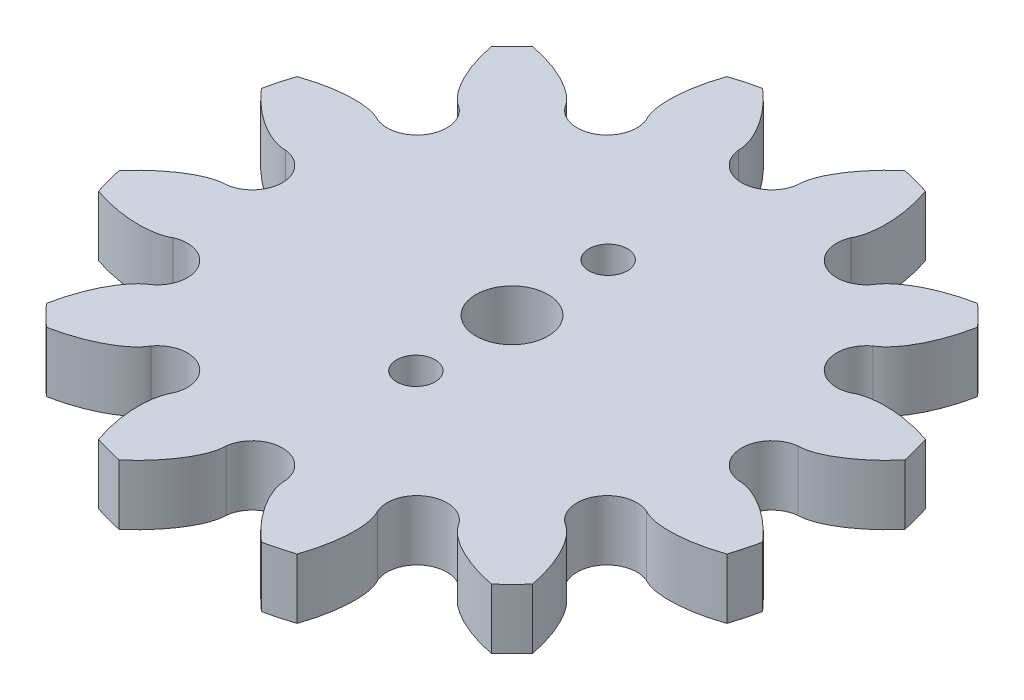
SolidWorks part; units mm, degrees
material "Gerais  - 6061-T6"
ref_plane "Plano frontal" through (0, 0, 0) normal (0, 0, 1) x (1, 0, 0)
ref_plane "Plano superior" through (0, 0, 0) normal (0, 1, 0) x (1, 0, 0)
ref_plane "Plano direito" through (0, 0, 0) normal (1, 0, 0) x (0, 0, -1)
ref_plane "Plano1" through (0, -5, 0) normal (0, -1, 0) x (1, 0, 0)
sketch "Esboço1" plane through (0, -5, 0) normal (0, -1, 0) x (1, 0, 0)
  arc A0 (-19.6917, 75.4926) -> (-17.2134, 71.2002) centre (-18.7058, 73.2002) cw
  arc A1 (-20.2254, 65.4903) -> (-18.5097, 63.7746) centre (0, 84) ccw
  arc A2 (-12.7998, 66.7866) -> (-8.5074, 64.3083) centre (-10.7998, 65.2942) cw
  arc A3 (-8.2609, 57.8575) -> (-5.9171, 57.2295) centre (0, 84) ccw
  arc A4 (-2.4783, 62.6928) -> (2.4783, 62.6928) centre (0, 62.4004) cw
  arc A5 (5.9171, 57.2295) -> (8.2609, 57.8575) centre (0, 84) ccw
  arc A6 (8.5074, 64.3083) -> (12.7998, 66.7866) centre (10.7998, 65.2942) cw
  arc A7 (18.5097, 63.7746) -> (20.2254, 65.4903) centre (0, 84) ccw
  arc A8 (17.2134, 71.2002) -> (19.6917, 75.4926) centre (18.7058, 73.2002) cw
  arc A9 (26.1425, 75.7391) -> (26.7705, 78.0829) centre (0, 84) ccw
  arc A10 (21.3072, 81.5217) -> (21.3072, 86.4783) centre (21.5996, 84) cw
  arc A11 (26.7705, 89.9171) -> (26.1425, 92.2609) centre (0, 84) ccw
  arc A12 (19.6917, 92.5074) -> (17.2134, 96.7998) centre (18.7058, 94.7998) cw
  arc A13 (20.2254, 102.5097) -> (18.5097, 104.2254) centre (0, 84) ccw
  arc A14 (12.7998, 101.2134) -> (8.5074, 103.6917) centre (10.7998, 102.7058) cw
  arc A15 (8.2609, 110.1425) -> (5.9171, 110.7705) centre (0, 84) ccw
  arc A16 (2.4783, 105.3072) -> (-2.4783, 105.3072) centre (0, 105.5996) cw
  arc A17 (-5.9171, 110.7705) -> (-8.2609, 110.1425) centre (0, 84) ccw
  arc A18 (-8.5074, 103.6917) -> (-12.7998, 101.2134) centre (-10.7998, 102.7058) cw
  arc A19 (-18.5097, 104.2254) -> (-20.2254, 102.5097) centre (0, 84) ccw
  arc A20 (-17.2134, 96.7998) -> (-19.6917, 92.5074) centre (-18.7058, 94.7998) cw
  arc A21 (-26.1425, 92.2609) -> (-26.7705, 89.9171) centre (0, 84) ccw
  arc A22 (-21.3072, 86.4783) -> (-21.3072, 81.5217) centre (-21.5996, 84) cw
  arc A23 (-26.7705, 78.0829) -> (-26.1425, 75.7391) centre (0, 84) ccw
  circle A24 centre (0, 84) radius 3 construction
  circle A25 centre (0, 92) radius 1.5 construction
  circle A26 centre (0, 76) radius 1.5 construction
  ellipse E0 centre (-17.6193, 65.5896) end of major axis (-19.0329, 59.7891) minor radius 2.5266 (-17.2134, 71.2002) -> (-20.2254, 65.4903) ccw
  ellipse E1 centre (-18.4104, 66.3807) end of major axis (-12.61, 67.7943) minor radius 2.5266 (-18.5097, 63.7746) -> (-12.7998, 66.7866) ccw
  ellipse E2 centre (-6.0536, 59.2464) end of major axis (-7.7295, 64.9766) minor radius 2.5266 (-8.5074, 64.3083) -> (-8.2609, 57.8575) ccw
  ellipse E3 centre (-7.1343, 59.536) end of major axis (-2.8177, 63.6604) minor radius 2.5266 (-5.9171, 57.2295) -> (-2.4783, 62.6928) ccw
  ellipse E4 centre (7.1343, 59.536) end of major axis (11.4508, 55.4116) minor radius 2.5266 (2.4783, 62.6928) -> (5.9171, 57.2295) ccw
  ellipse E5 centre (6.0536, 59.2464) end of major axis (7.7295, 64.9766) minor radius 2.5266 (8.2609, 57.8575) -> (8.5074, 64.3083) ccw
  ellipse E6 centre (18.4104, 66.3807) end of major axis (24.2109, 64.9671) minor radius 2.5266 (12.7998, 66.7866) -> (18.5097, 63.7746) ccw
  ellipse E7 centre (17.6193, 65.5896) end of major axis (16.2057, 71.39) minor radius 2.5266 (20.2254, 65.4903) -> (17.2134, 71.2002) ccw
  ellipse E8 centre (24.7536, 77.9464) end of major axis (30.4837, 79.6224) minor radius 2.5266 (19.6917, 75.4926) -> (26.1425, 75.7391) ccw
  ellipse E9 centre (24.464, 76.8657) end of major axis (20.3396, 81.1823) minor radius 2.5266 (26.7705, 78.0829) -> (21.3072, 81.5217) ccw
  ellipse E10 centre (24.464, 91.1343) end of major axis (20.3396, 86.8177) minor radius 2.5266 (21.3072, 86.4783) -> (26.7705, 89.9171) ccw
  ellipse E11 centre (24.7536, 90.0536) end of major axis (30.4837, 88.3776) minor radius 2.5266 (26.1425, 92.2609) -> (19.6917, 92.5074) ccw
  ellipse E12 centre (17.6193, 102.4104) end of major axis (16.2057, 96.61) minor radius 2.5266 (17.2134, 96.7998) -> (20.2254, 102.5097) ccw
  ellipse E13 centre (18.4104, 101.6193) end of major axis (12.61, 100.2057) minor radius 2.5266 (18.5097, 104.2254) -> (12.7998, 101.2134) ccw
  ellipse E14 centre (6.0536, 108.7536) end of major axis (7.7295, 103.0234) minor radius 2.5266 (8.5074, 103.6917) -> (8.2609, 110.1425) ccw
  ellipse E15 centre (7.1343, 108.464) end of major axis (11.4508, 112.5884) minor radius 2.5266 (5.9171, 110.7705) -> (2.4783, 105.3072) ccw
  ellipse E16 centre (-7.1343, 108.464) end of major axis (-2.8177, 104.3396) minor radius 2.5266 (-2.4783, 105.3072) -> (-5.9171, 110.7705) ccw
  ellipse E17 centre (-6.0536, 108.7536) end of major axis (-4.3776, 114.4837) minor radius 2.5266 (-8.2609, 110.1425) -> (-8.5074, 103.6917) ccw
  ellipse E18 centre (-18.4104, 101.6193) end of major axis (-12.61, 100.2057) minor radius 2.5266 (-12.7998, 101.2134) -> (-18.5097, 104.2254) ccw
  ellipse E19 centre (-17.6193, 102.4104) end of major axis (-19.0329, 108.2109) minor radius 2.5266 (-20.2254, 102.5097) -> (-17.2134, 96.7998) ccw
  ellipse E20 centre (-24.7536, 90.0536) end of major axis (-19.0234, 91.7295) minor radius 2.5266 (-19.6917, 92.5074) -> (-26.1425, 92.2609) ccw
  ellipse E21 centre (-24.464, 91.1343) end of major axis (-28.5884, 95.4508) minor radius 2.5266 (-26.7705, 89.9171) -> (-21.3072, 86.4783) ccw
  ellipse E22 centre (-24.464, 76.8657) end of major axis (-28.5884, 72.5492) minor radius 2.5266 (-21.3072, 81.5217) -> (-26.7705, 78.0829) ccw
  ellipse E23 centre (-24.7536, 77.9464) end of major axis (-19.0234, 76.2705) minor radius 2.5266 (-26.1425, 75.7391) -> (-19.6917, 75.4926) ccw
  point P3 (-17.6193, 65.5896)
  point P4 (-15.1646, 64.9913)
  point P5 (-19.0329, 59.7891)
  point P6 (-17.2134, 71.2002)
  point P7 (-20.2254, 65.4903)
  point P8 (-19.0162, 69.0502)
  point P9 (-16.2225, 62.129)
  point P18 (-18.4104, 66.3807)
  point P19 (-12.61, 67.7943)
  point P20 (-19.0087, 68.8354)
  point P21 (-18.5097, 63.7746)
  point P22 (-12.7998, 66.7866)
  point P23 (-14.9498, 64.9838)
  point P24 (-21.871, 67.7775)
  point P33 (-6.0536, 59.2464)
  point P34 (-3.6286, 59.9557)
  point P35 (-4.3776, 53.5163)
  point P36 (-8.5074, 64.3083)
  point P37 (-8.2609, 57.8575)
  point P38 (-8.9936, 61.545)
  point P39 (-3.1135, 56.9479)
  point P47 (-7.1343, 59.536)
  point P48 (-2.8177, 63.6604)
  point P49 (-8.8797, 61.3628)
  point P50 (-5.9171, 57.2295)
  point P51 (-2.4783, 62.6928)
  point P52 (-3.4389, 60.0566)
  point P53 (-10.8296, 59.0154)
  point P62 (7.1343, 59.536)
  point P63 (11.4508, 55.4116)
  point P64 (5.3888, 57.7093)
  point P65 (2.4783, 62.6928)
  point P66 (5.9171, 57.2295)
  point P67 (3.4389, 60.0566)
  point P68 (10.8296, 59.0154)
  point P76 (6.0536, 59.2464)
  point P77 (8.4785, 58.5372)
  point P78 (7.7295, 64.9766)
  point P79 (8.2609, 57.8575)
  point P80 (8.5074, 64.3083)
  point P81 (8.9936, 61.545)
  point P82 (3.1135, 56.9479)
  point P91 (18.4104, 66.3807)
  point P92 (24.2109, 64.9671)
  point P93 (17.8122, 63.926)
  point P94 (12.7998, 66.7866)
  point P95 (18.5097, 63.7746)
  point P96 (14.9498, 64.9838)
  point P97 (21.871, 67.7775)
  point P105 (17.6193, 65.5896)
  point P106 (20.074, 66.1878)
  point P107 (16.2057, 71.39)
  point P108 (20.2254, 65.4903)
  point P109 (17.2134, 71.2002)
  point P110 (19.0162, 69.0502)
  point P111 (16.2225, 62.129)
  point P120 (24.7536, 77.9464)
  point P121 (30.4837, 79.6224)
  point P122 (25.4628, 75.5215)
  point P123 (19.6917, 75.4926)
  point P124 (26.1425, 75.7391)
  point P125 (22.455, 75.0064)
  point P126 (27.0521, 80.8865)
  point P134 (24.464, 76.8657)
  point P135 (26.2907, 78.6112)
  point P136 (20.3396, 81.1823)
  point P137 (26.7705, 78.0829)
  point P138 (21.3072, 81.5217)
  point P139 (23.9434, 80.5611)
  point P140 (24.9846, 73.1704)
  point P149 (24.464, 91.1343)
  point P150 (26.2907, 89.3888)
  point P151 (20.3396, 86.8177)
  point P152 (21.3072, 86.4783)
  point P153 (26.7705, 89.9171)
  point P154 (23.9434, 87.4389)
  point P155 (24.9846, 94.8296)
  point P163 (24.7536, 90.0536)
  point P164 (30.4837, 88.3776)
  point P165 (25.4628, 92.4785)
  point P166 (26.1425, 92.2609)
  point P167 (19.6917, 92.5074)
  point P168 (22.455, 92.9936)
  point P169 (27.0521, 87.1135)
  point P178 (17.6193, 102.4104)
  point P179 (20.074, 101.8122)
  point P180 (16.2057, 96.61)
  point P181 (17.2134, 96.7998)
  point P182 (20.2254, 102.5097)
  point P183 (19.0162, 98.9498)
  point P184 (16.2225, 105.871)
  point P192 (18.4104, 101.6193)
  point P193 (24.2109, 103.0329)
  point P194 (17.8122, 104.074)
  point P195 (18.5097, 104.2254)
  point P196 (12.7998, 101.2134)
  point P197 (14.9498, 103.0162)
  point P198 (21.871, 100.2225)
  point P207 (6.0536, 108.7536)
  point P208 (8.4785, 109.4628)
  point P209 (7.7295, 103.0234)
  point P210 (8.5074, 103.6917)
  point P211 (8.2609, 110.1425)
  point P212 (8.9936, 106.455)
  point P213 (3.1135, 111.0521)
  point P221 (7.1343, 108.464)
  point P222 (11.4508, 112.5884)
  point P223 (5.3888, 110.2907)
  point P224 (5.9171, 110.7705)
  point P225 (2.4783, 105.3072)
  point P226 (3.4389, 107.9434)
  point P227 (10.8296, 108.9846)
  point P236 (-7.1343, 108.464)
  point P237 (-2.8177, 104.3396)
  point P238 (-8.8797, 106.6372)
  point P239 (-2.4783, 105.3072)
  point P240 (-5.9171, 110.7705)
  point P241 (-3.4389, 107.9434)
  point P242 (-10.8296, 108.9846)
  point P250 (-6.0536, 108.7536)
  point P251 (-3.6286, 108.0443)
  point P252 (-4.3776, 114.4837)
  point P253 (-8.2609, 110.1425)
  point P254 (-8.5074, 103.6917)
  point P255 (-8.9936, 106.455)
  point P256 (-3.1135, 111.0521)
  point P265 (-18.4104, 101.6193)
  point P266 (-12.61, 100.2057)
  point P267 (-19.0087, 99.1646)
  point P268 (-12.7998, 101.2134)
  point P269 (-18.5097, 104.2254)
  point P270 (-14.9498, 103.0162)
  point P271 (-21.871, 100.2225)
  point P279 (-17.6193, 102.4104)
  point P280 (-15.1646, 103.0087)
  point P281 (-19.0329, 108.2109)
  point P282 (-20.2254, 102.5097)
  point P283 (-17.2134, 96.7998)
  point P284 (-19.0162, 98.9498)
  point P285 (-16.2225, 105.871)
  point P294 (-24.7536, 90.0536)
  point P295 (-19.0234, 91.7295)
  point P296 (-24.0443, 87.6286)
  point P297 (-19.6917, 92.5074)
  point P298 (-26.1425, 92.2609)
  point P299 (-22.455, 92.9936)
  point P300 (-27.0521, 87.1135)
  point P308 (-24.464, 91.1343)
  point P309 (-22.6372, 92.8797)
  point P310 (-28.5884, 95.4508)
  point P311 (-26.7705, 89.9171)
  point P312 (-21.3072, 86.4783)
  point P313 (-23.9434, 87.4389)
  point P314 (-24.9846, 94.8296)
  point P323 (-24.464, 76.8657)
  point P324 (-22.6372, 75.1203)
  point P325 (-28.5884, 72.5492)
  point P326 (-21.3072, 81.5217)
  point P327 (-26.7705, 78.0829)
  point P328 (-23.9434, 80.5611)
  point P329 (-24.9846, 73.1704)
  point P337 (-24.7536, 77.9464)
  point P338 (-19.0234, 76.2705)
  point P339 (-24.0443, 80.3714)
  point P340 (-26.1425, 75.7391)
  point P341 (-19.6917, 75.4926)
  point P342 (-22.455, 75.0064)
  point P343 (-27.0521, 80.8865)
extrude "Ressalto-extrusão1" add sketch "Esboço1" against normal blind 5
sketch "Esboço3" plane through (0, -5, 0) normal (0, -1, 0) x (1, 0, 0)
  line L0 (0, 92) -> (0, 76) construction
  circle A0 centre (0, 84) radius 3
  circle A1 centre (0, 92) radius 1.6
  circle A2 centre (0, 76) radius 1.6
  dimension "D1" = 6
  dimension "D3" = 3.2
  dimension "D2" = 8
extrude "Corte-extrusão1" cut sketch "Esboço3" against normal blind 10
